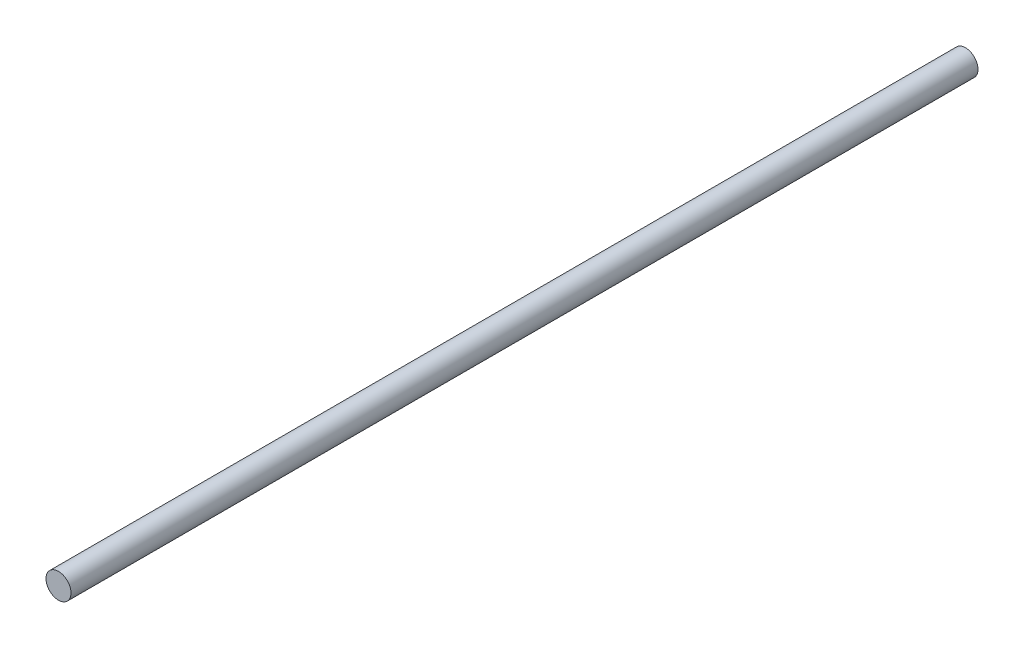
SolidWorks part; units mm, degrees
material "Plain Carbon Steel"
ref_plane "Front Plane" through (0, 0, 0) normal (0, 0, 1) x (1, 0, 0)
ref_plane "Top Plane" through (0, 0, 0) normal (0, 1, 0) x (1, 0, 0)
ref_plane "Right Plane" through (0, 0, 0) normal (1, 0, 0) x (0, 0, -1)
sketch "Sketch1" plane through (0, 0, 0) normal (0, 0, 1) x (1, 0, 0)
  circle A0 centre (0, 0) radius 4
  dimension "D1" = 8
extrude "Boss-Extrude1" add sketch "Sketch1" along normal blind 290
